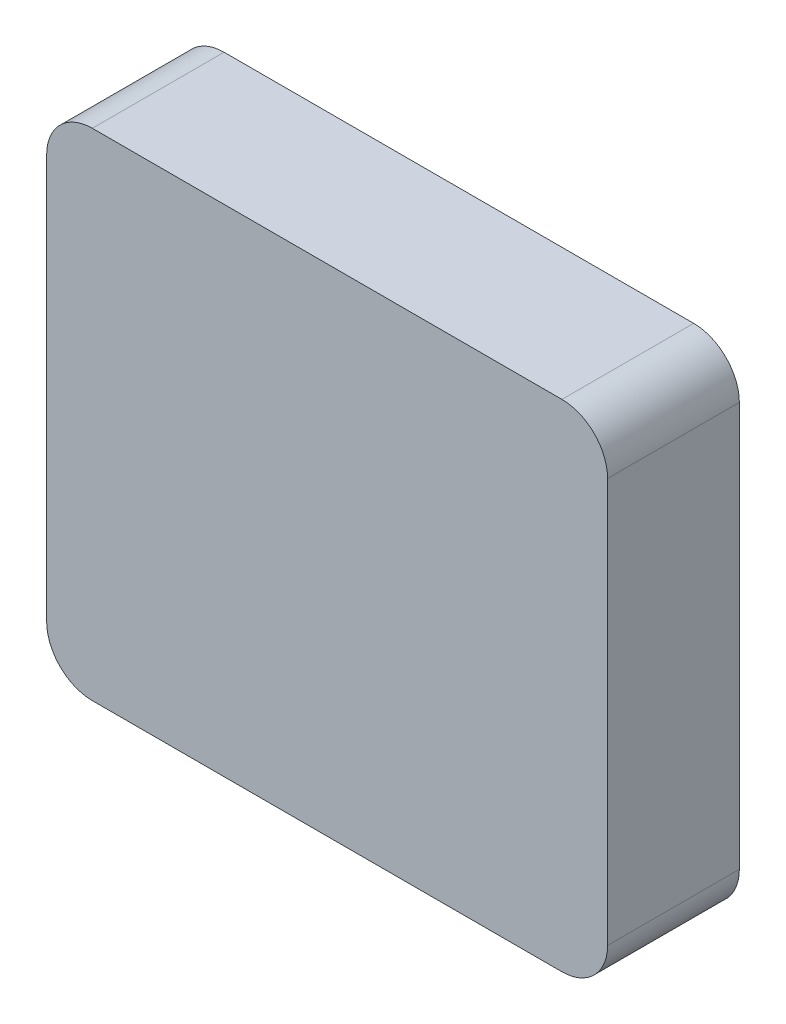
SolidWorks part; units mm, degrees
ref_plane "Front Plane" through (0, 0, 0) normal (0, 0, 1) x (1, 0, 0)
ref_plane "Top Plane" through (0, 0, 0) normal (0, 1, 0) x (1, 0, 0)
ref_plane "Right Plane" through (0, 0, 0) normal (1, 0, 0) x (0, 0, -1)
sketch "Sketch1" plane through (0, 0, 0) normal (0, 0, 1) x (1, 0, 0)
  line L0 (-175, 300) -> (-175, 340) construction
  line L1 (0, 0) -> (-350, 0)
  line L2 (0, 0) -> (0, 300)
  line L3 (0, 300) -> (-350, 300)
  line L4 (-350, 0) -> (-350, 300)
  line L5 (-355, 340) -> (5, 340)
  line L6 (-390, 305) -> (-390, -5)
  line L7 (-355, -40) -> (5, -40)
  line L8 (40, 305) -> (40, -5)
  arc A0 (5, -40) -> (40, -5) centre (5, -5) ccw
  arc A1 (5, 340) -> (40, 305) centre (5, 305) cw
  arc A2 (-355, 340) -> (-390, 305) centre (-355, 305) ccw
  arc A3 (-390, -5) -> (-355, -40) centre (-355, -5) ccw
  dimension "D5" = 35
  dimension "D4" = 35
  dimension "D1" = 350
  dimension "D2" = 300
  dimension "D3" = 40
  dimension "D6" = 40
  dimension "D7" = 40
extrude "Boss-Extrude1" add sketch "Sketch1" along normal blind 100
sketch "Sketch2" plane through (0, 0, 100) normal (0, 0, 1) x (1, 0, 0)
  line L0 (-355, -40) -> (5, -40) construction
  line L1 (-390, 305) -> (-390, -5) construction
  line L2 (5, 340) -> (-355, 340) construction
  line L3 (40, -5) -> (40, 305) construction
  line L4 (-355, -40) -> (5, -40)
  line L5 (-390, 305) -> (-390, -5)
  line L6 (5, 340) -> (-355, 340)
  line L7 (40, -5) -> (40, 305)
  arc A0 (5, -40) -> (40, -5) centre (5, -5) ccw construction
  arc A1 (-390, -5) -> (-355, -40) centre (-355, -5) ccw construction
  arc A2 (-355, 340) -> (-390, 305) centre (-355, 305) ccw construction
  arc A3 (40, 305) -> (5, 340) centre (5, 305) ccw construction
  arc A4 (5, -40) -> (40, -5) centre (5, -5) ccw
  arc A5 (-390, -5) -> (-355, -40) centre (-355, -5) ccw
  arc A6 (-355, 340) -> (-390, 305) centre (-355, 305) ccw
  arc A7 (40, 305) -> (5, 340) centre (5, 305) ccw
extrude "Boss-Extrude2" add sketch "Sketch2" along normal blind 1
